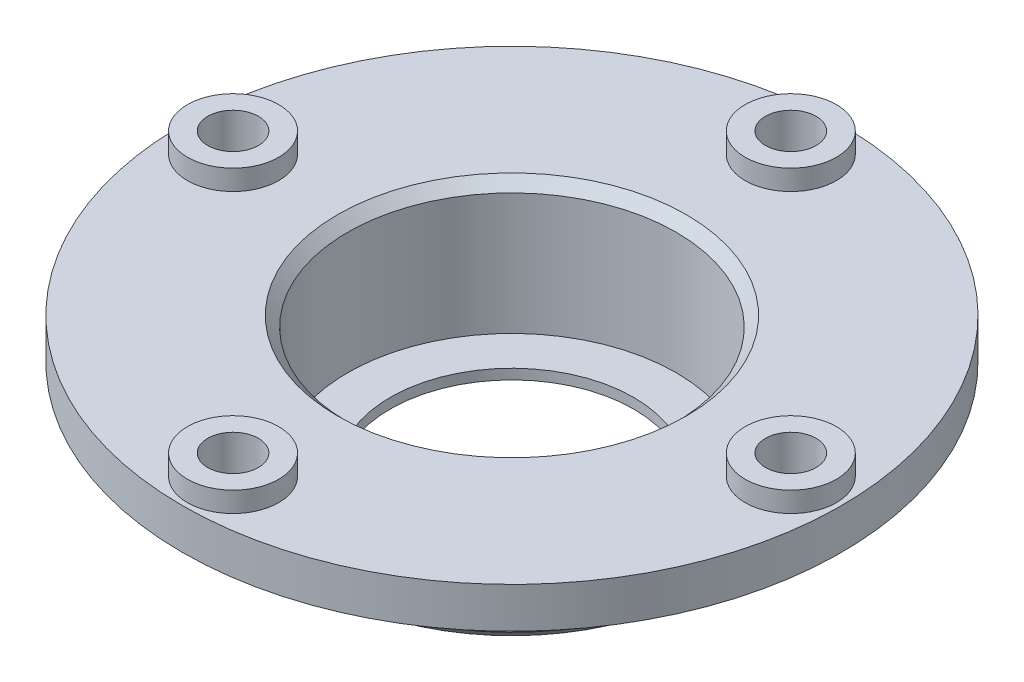
SolidWorks part; units mm, degrees
ref_plane "Front Plane" through (0, 0, 0) normal (0, 0, 1) x (1, 0, 0)
ref_plane "Top Plane" through (0, 0, 0) normal (0, 1, 0) x (1, 0, 0)
ref_plane "Right Plane" through (0, 0, 0) normal (1, 0, 0) x (0, 0, -1)
sketch "Sketch1" plane through (0, 0, 0) normal (0, 1, 0) x (1, 0, 0)
  circle A0 centre (0, 0) radius 19.9
  circle A1 centre (0, 0) radius 16.2
  dimension "D1" = 39.8
  dimension "D2" = 32.4
extrude "Boss-Extrude1" add sketch "Sketch1" along normal blind 9
sketch "Sketch2" plane through (0, 9, 0) normal (0, 1, 0) x (1, 0, 0)
  circle A0 centre (0, 0) radius 16.2 construction
  circle A1 centre (0, 0) radius 16.2
  circle A2 centre (0, 0) radius 22
  dimension "D1" = 44
extrude "Boss-Extrude2" add sketch "Sketch2" along normal blind 1
sketch "Sketch3" plane through (0, 10, 0) normal (0, 1, 0) x (1, 0, 0)
  circle A0 centre (0, 0) radius 16.2 construction
  circle A1 centre (0, 0) radius 16.2
  circle A2 centre (0, 0) radius 32.5
  dimension "D1" = 65
extrude "Boss-Extrude3" add sketch "Sketch3" along normal blind 1
sketch "Sketch6" plane through (0, 11, 0) normal (0, 1, 0) x (1, 0, 0)
  circle A0 centre (0, 27.5) radius 2.5
  circle A2 centre (27.5, 0) radius 2.5
  circle A3 centre (0, -27.5) radius 2.5
  circle A4 centre (-27.5, 0) radius 2.5
  circle A5 centre (0, 0) radius 32.5 construction
  circle A6 centre (0, 0) radius 16.2
  circle A7 centre (0, 0) radius 16.2
  circle A8 centre (0, 0) radius 32.5
  point P13 (0, 0)
  dimension "D2" = 5
  dimension "D1" = 27.5
  dimension "D4" = 0
  dimension "D3" = 4
extrude "Boss-Extrude6" add sketch "Sketch6" along normal blind 3
sketch "Sketch7" plane through (0, 14, 0) normal (0, 1, 0) x (1, 0, 0)
  circle A0 centre (0, -27.5) radius 4.5
  circle A1 centre (0, -27.5) radius 2.5
  circle A2 centre (0, -27.5) radius 2.5
  circle A3 centre (0, 27.5) radius 2.5
  circle A4 centre (0, 27.5) radius 2.5
  circle A5 centre (27.5, 0) radius 2.5
  circle A6 centre (27.5, 0) radius 2.5
  circle A7 centre (-27.5, 0) radius 2.5
  circle A8 centre (-27.5, 0) radius 2.5
  circle A9 centre (0, 27.5) radius 4.5
  circle A10 centre (27.5, 0) radius 4.5
  circle A11 centre (-27.5, 0) radius 4.5
  dimension "D1" = 0
  dimension "D2" = 0
  dimension "D3" = 0
  dimension "D4" = 0
  dimension "D5" = 2
extrude "Boss-Extrude7" add sketch "Sketch7" along normal blind 2
sketch "Sketch8" plane through (0, 0, 0) normal (0, -1, 0) x (-1, 0, 0)
  circle A0 centre (0, 0) radius 12
  circle A1 centre (0, 0) radius 16.2
  circle A2 centre (0, 0) radius 16.2
  dimension "D2" = 24
  dimension "D1" = 0
extrude "Boss-Extrude8" add sketch "Sketch8" against normal blind 1
sketch "Sketch9" plane through (0, 11, 0) normal (0, 1, 0) x (1, 0, 0)
  circle A0 centre (0, -27.5) radius 2.5 construction
  circle A1 centre (27.5, 0) radius 2.5 construction
  circle A2 centre (0, 27.5) radius 2.5 construction
  circle A3 centre (-27.5, 0) radius 2.5 construction
  circle A4 centre (0, -27.5) radius 2.5
  circle A5 centre (27.5, 0) radius 2.5
  circle A6 centre (0, 27.5) radius 2.5
  circle A7 centre (-27.5, 0) radius 2.5
extrude "Cut-Extrude1" cut sketch "Sketch9" against normal blind 10
chamfer "Chamfer1" distance 1 angle 45 1 edges at (0, 14, 16.2)
chamfer "Chamfer2" distance 1 angle 45 1 edges at (0, 0, 19.9)
